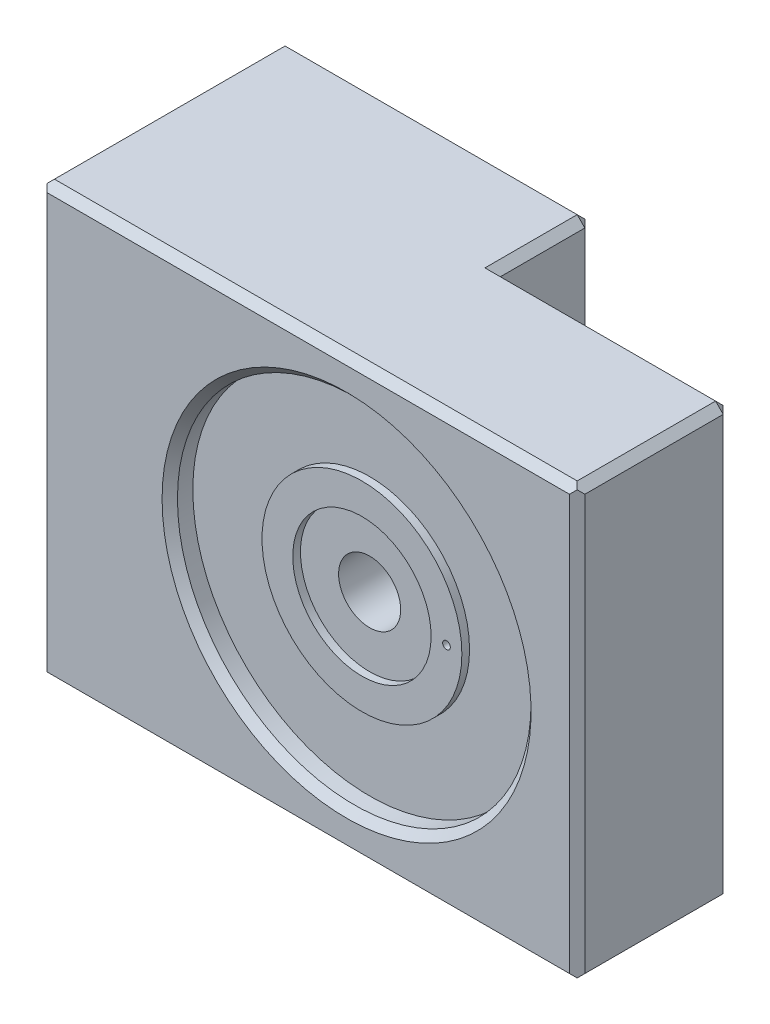
SolidWorks part; units mm, degrees
ref_plane "Front Plane" through (0, 0, 0) normal (0, 0, 1) x (1, 0, 0)
ref_plane "Top Plane" through (0, 0, 0) normal (0, 1, 0) x (1, 0, 0)
ref_plane "Right Plane" through (0, 0, 0) normal (1, 0, 0) x (0, 0, -1)
sketch "Sketch1" plane through (0, 0, 0) normal (0, 0, 1) x (1, 0, 0)
  line L0 (17.5, -14) -> (17.5, 14)
  line L1 (17.5, -14) -> (-17.5, -14)
  line L2 (17.5, 14) -> (-17.5, 14)
  line L3 (-17.5, -14) -> (-17.5, 14)
  line L4 (17.5, -14) -> (-17.5, 14) construction
  line L5 (17.5, 14) -> (-17.5, -14) construction
  circle A0 centre (10.3147, 0) radius 11.05 construction
  point P1 (0, 0)
  dimension "D1" = 22.1
  dimension "D2" = 35
  dimension "D3" = 28
extrude "Boss-Extrude1" add sketch "Sketch1" along normal blind 16 contours L0 L1 L3 L2
sketch "Sketch2" plane through (0, 0, 16) normal (0, 0, 1) x (1, 0, 0)
  line L0 (17.5, -14) -> (17.5, 14) construction
  circle A0 centre (2.5, 0) radius 11.5
  dimension "D1" = 23
  dimension "D2" = 15
extrude "Cut-Extrude1" cut sketch "Sketch2" against normal blind 1.5
sketch "Sketch3" plane through (0, 0, 14.5) normal (0, 0, 1) x (1, 0, 0)
  circle A0 centre (2.5, 0) radius 2.0193
  dimension "D1" = 4.0386
extrude "Cut-Extrude2" cut sketch "Sketch3" against normal blind 7
sketch "Sketch4" plane through (-17.5, 0, 0) normal (-1, 0, 0) x (0, 0, 1)
  line L0 (16, -14) -> (0, -14) construction
  circle A0 centre (8, 0) radius 4.2164
  point P4 (8, -14)
  dimension "D1" = 8.4328
extrude "Cut-Extrude3" cut sketch "Sketch4" against normal blind 13.318
sketch "Sketch5" plane through (-4.182, 0, 0) normal (-1, 0, 0) x (0, 0, 1)
  circle A0 centre (8, 0) radius 1.2446
  dimension "D1" = 2.4892
extrude "Cut-Extrude4" cut sketch "Sketch5" against normal up to surface (4.6627 mm away)
sketch "Sketch6" plane through (0, 0, 14.5) normal (0, 0, 1) x (1, 0, 0)
  circle A2 centre (2.5, 0) radius 4.5
  circle A3 centre (2.5, 0) radius 6.5
  dimension "D1" = 9
  dimension "D2" = 13
extrude "Boss-Extrude2" add sketch "Sketch6" along normal blind 0.5
sketch "Sketch7" plane through (0, 0, 15) normal (0, 0, 1) x (1, 0, 0)
  line L0 (7, 0) -> (9, 0) construction
  circle A0 centre (8, 0) radius 0.5
  circle A1 centre (2.5, 0) radius 4.5 construction
  circle A2 centre (2.5, 0) radius 6.5 construction
  point P9 (8, 0)
  dimension "D1" = 1
extrude "Cut-Extrude5" cut sketch "Sketch7" against normal blind 9
sketch "Sketch15" plane through (0, 0, 0) normal (0, 0, -1) x (-1, 0, 0)
  line L0 (-2.5, -14) -> (-2.5, 14)
  line L1 (-17.5, -14) -> (17.5, -14) construction
  line L2 (-17.5, 14) -> (17.5, 14) construction
  line L3 (-2.5, 14) -> (-17.5, 14)
  line L4 (-17.5, 14) -> (-17.5, -14)
  line L5 (-17.5, -14) -> (-2.5, -14)
  dimension "D1" = 15
extrude "Cut-Extrude9" cut sketch "Sketch15" against normal blind 6
ref_plane "Plane2" through (0, 0, 0) normal (0, 1, 0) x (1, 0, 0)
sketch "Sketch16" plane through (0, 0, 6) normal (0, 0, -1) x (-1, 0, 0)
  circle A0 centre (-8, 0) radius 0.25
  circle A1 centre (-8, 0) radius 1.5875
  dimension "D1" = 3.175
  dimension "D2" = 0.5
extrude "Boss-Extrude4" add sketch "Sketch16" along normal blind 3
sketch "Sketch17" plane through (0, 0, 6) normal (0, 0, 1) x (1, 0, 0)
  circle A0 centre (8, 0) radius 0.25
  circle A1 centre (8, 0) radius 0.516
extrude "Boss-Extrude5" add sketch "Sketch17" along normal up to surface (9 mm away) up to face at (8.5, 0, 15)
chamfer "Chamfer5" distance 0.5 angle 45 5 edges at (17.5, 0, 16) (0, 14, 16) (-17.5, 0, 16) (0, -14, 16) (14, 0, 16)
chamfer "Chamfer6" distance 0.2 angle 45 1 edges at (6.4125, 0, 3)
sketch "Sketch18" plane through (0, 0, 0) normal (0, 1, 0) x (1, 0, 0)
  line L0 (6.4008, -3.7198) -> (3.2258, -3.7198)
  dimension "D1" = 3.175
chamfer "Chamfer7" distance 0.5 angle 45 13 edges at (10, -14, 6) (2.5, 0, 0) (17.5, -14, 10.75) (17.5, 0, 6) (17.5, 14, 10.75) (10, 14, 6) (2.5, 14, 3) (-7.5, 14, 0) (-17.5, 14, 7.75) (-17.5, 0, 0) (-17.5, -14, 7.75) (-7.5, -14, 0) (2.5, -14, 3)
